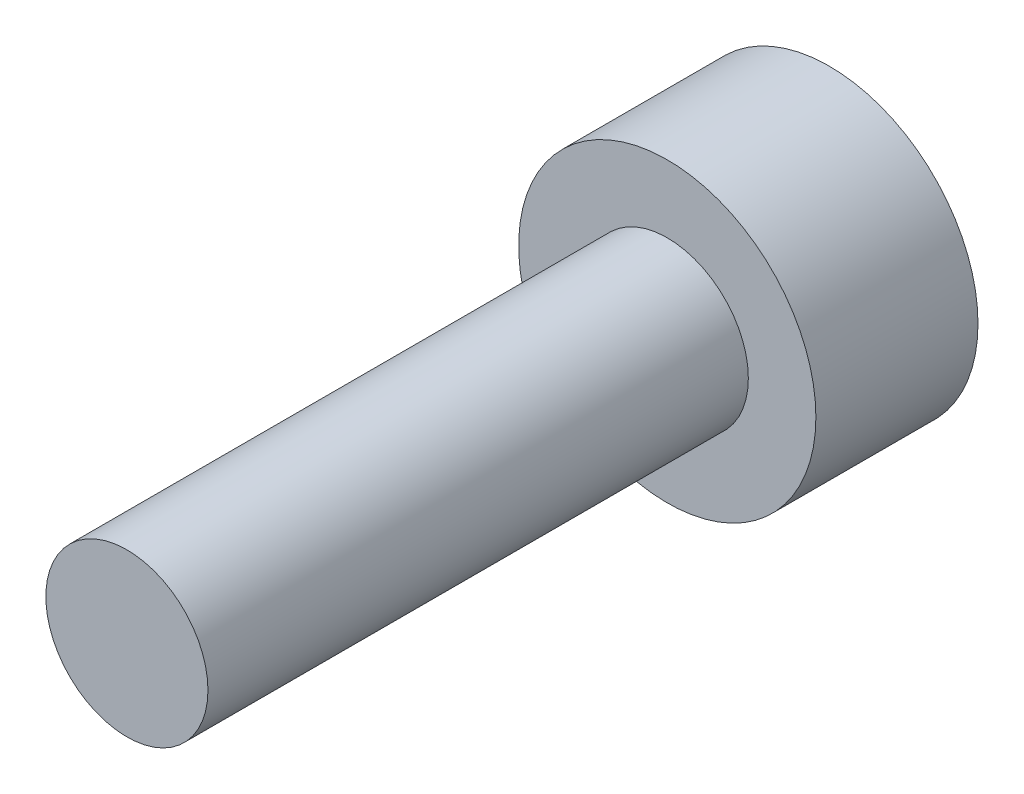
SolidWorks part; units mm, degrees
ref_plane "Plano frontal" through (0, 0, 0) normal (0, 0, 1) x (1, 0, 0)
ref_plane "Plano superior" through (0, 0, 0) normal (0, 1, 0) x (1, 0, 0)
ref_plane "Plano direito" through (0, 0, 0) normal (1, 0, 0) x (0, 0, -1)
sketch "Esboço1" plane through (0, 0, 0) normal (0, 1, 0) x (1, 0, 0)
  line L0 (0, 0) -> (2.75, 0)
  line L1 (2.75, 0) -> (2.75, -3)
  line L2 (2.75, -3) -> (1.5, -3)
  line L3 (0, -3) -> (0, 0)
  line L5 (1.5, -3) -> (1.5, -13)
  line L6 (1.5, -13) -> (0, -13)
  line L7 (0, -13) -> (0, -3)
revolve "Revolução1" add sketch "Esboço1" angle 360 about L3
sketch "Esboço2" plane through (0, 0, 0) normal (0, 0, -1) x (-1, 0, 0)
  line L1 (1.7321, 0) -> (0.866, 1.5)
  line L2 (0.866, 1.5) -> (-0.866, 1.5)
  line L3 (-0.866, 1.5) -> (-1.7321, 0)
  line L4 (-1.7321, 0) -> (-0.866, -1.5)
  line L5 (-0.866, -1.5) -> (0.866, -1.5)
  line L6 (0.866, -1.5) -> (1.7321, 0)
  circle A0 centre (0, 0) radius 1.5 construction
extrude "Corte-extrusão1" cut sketch "Esboço2" against normal blind 1.5
